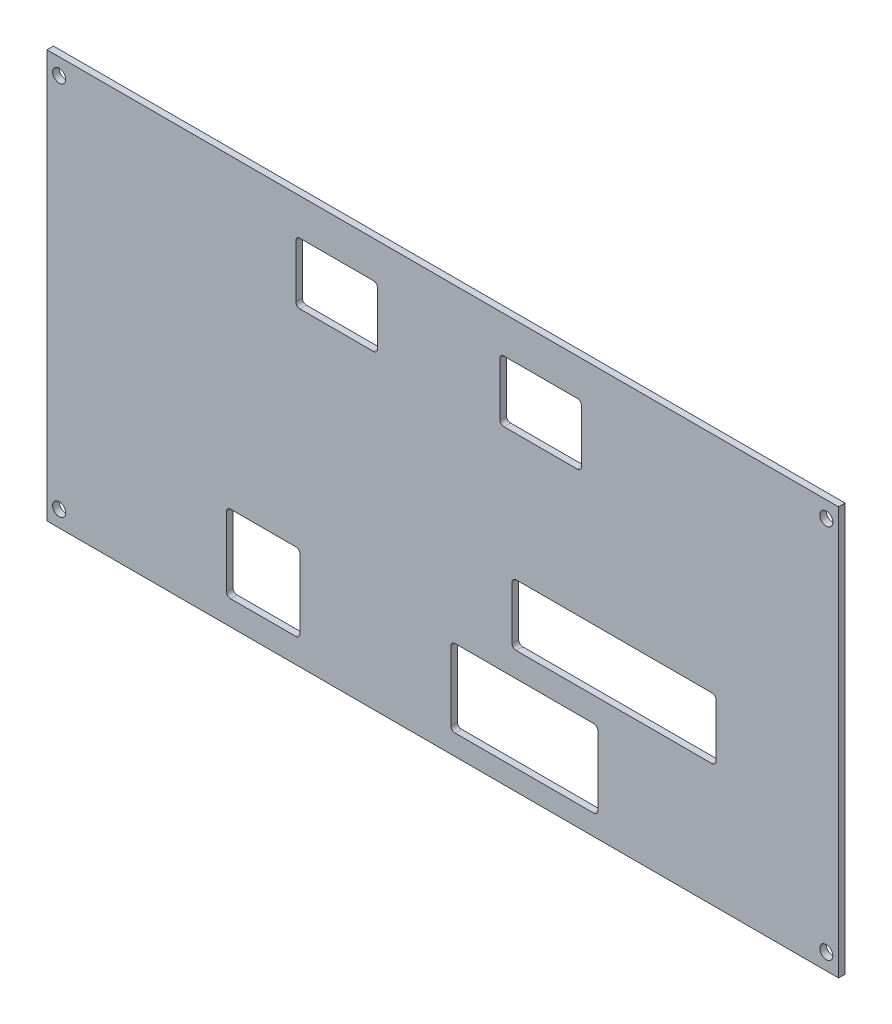
SolidWorks part; units mm, degrees
ref_plane "Plan de face" through (0, 0, 0) normal (0, 0, 1) x (1, 0, 0)
ref_plane "Plan de dessus" through (0, 0, 0) normal (0, 1, 0) x (1, 0, 0)
ref_plane "Plan de droite" through (0, 0, 0) normal (1, 0, 0) x (0, 0, -1)
sketch "Esquisse1" plane through (0, 0, 0) normal (0, 0, 1) x (1, 0, 0)
  line L1 (0, 0) -> (194, 0)
  line L2 (0, 0) -> (0, 100)
  line L3 (0, 100) -> (194, 100)
  line L4 (194, 0) -> (194, 100)
extrude "Boss.-Extru.1" add sketch "Esquisse1" along normal blind 1.6
sketch "Esquisse2" plane through (0, 0, 1.6) normal (0, 0, 1) x (1, 0, 0)
  line L0 (0, 100) -> (0, 0) construction
  line L1 (194, 0) -> (194, 100) construction
  line L2 (194, 100) -> (0, 100) construction
  line L3 (0, 0) -> (194, 0) construction
  line L5 (45, 25) -> (61, 25)
  line L6 (44, 24) -> (44, 7)
  line L7 (45, 6) -> (61, 6)
  line L8 (62, 24) -> (62, 7)
  line L9 (62, 91) -> (80, 91)
  line L10 (61, 90) -> (61, 77)
  line L11 (62, 76) -> (80, 76)
  line L12 (81, 90) -> (81, 77)
  line L13 (112, 91) -> (130, 91)
  line L14 (111, 90) -> (111, 77)
  line L15 (112, 76) -> (130, 76)
  line L16 (131, 90) -> (131, 77)
  line L17 (115, 45) -> (163, 45)
  line L18 (114, 44) -> (114, 31)
  line L19 (115, 30) -> (163, 30)
  line L20 (164, 44) -> (164, 31)
  line L21 (100, 24) -> (134, 24)
  line L22 (99, 23) -> (99, 6)
  line L23 (100, 5) -> (134, 5)
  line L24 (135, 23) -> (135, 6)
  circle A0 centre (3, 96) radius 1.6
  circle A1 centre (191, 96) radius 1.6
  circle A2 centre (191, 4) radius 1.6
  circle A3 centre (3, 4) radius 1.6
  arc A4 (44, 7) -> (45, 6) centre (45, 7) ccw
  arc A5 (61, 6) -> (62, 7) centre (61, 7) ccw
  arc A6 (61, 25) -> (62, 24) centre (61, 24) cw
  arc A7 (45, 25) -> (44, 24) centre (45, 24) ccw
  arc A8 (100, 24) -> (99, 23) centre (100, 23) ccw
  arc A9 (99, 6) -> (100, 5) centre (100, 6) ccw
  arc A10 (134, 5) -> (135, 6) centre (134, 6) ccw
  arc A11 (163, 45) -> (164, 44) centre (163, 44) cw
  arc A12 (163, 30) -> (164, 31) centre (163, 31) ccw
  arc A13 (134, 24) -> (135, 23) centre (134, 23) cw
  arc A14 (114, 31) -> (115, 30) centre (115, 31) ccw
  arc A15 (115, 45) -> (114, 44) centre (115, 44) ccw
  arc A16 (111, 77) -> (112, 76) centre (112, 77) ccw
  arc A17 (130, 76) -> (131, 77) centre (130, 77) ccw
  arc A18 (130, 91) -> (131, 90) centre (130, 90) cw
  arc A19 (112, 91) -> (111, 90) centre (112, 90) ccw
  arc A20 (61, 77) -> (62, 76) centre (62, 77) ccw
  arc A21 (80, 76) -> (81, 77) centre (80, 77) ccw
  arc A22 (80, 91) -> (81, 90) centre (80, 90) cw
  arc A23 (62, 91) -> (61, 90) centre (62, 90) ccw
  point P38 (44, 6)
  point P43 (62, 25)
  point P46 (44, 25)
  point P49 (99, 24)
  point P52 (99, 5)
  point P55 (135, 5)
  point P58 (164, 45)
  point P65 (114, 30)
  point P68 (114, 45)
  point P71 (111, 76)
  point P74 (131, 76)
  point P79 (111, 91)
  point P82 (61, 76)
  point P85 (81, 76)
  point P90 (61, 91)
  dimension "D1" = 3
  dimension "D27" = 1
  dimension "D2" = 3
  dimension "D3" = 3
  dimension "D4" = 3
  dimension "D5" = 4
  dimension "D6" = 4
  dimension "D7" = 4
  dimension "D8" = 4
  dimension "D9" = 19
  dimension "D10" = 18
  dimension "D11" = 20
  dimension "D12" = 15
  dimension "D13" = 15
  dimension "D14" = 20
  dimension "D15" = 50
  dimension "D16" = 9
  dimension "D17" = 9
  dimension "D18" = 61
  dimension "D19" = 50
  dimension "D20" = 15
  dimension "D21" = 30
  dimension "D22" = 30
  dimension "D23" = 36
  dimension "D24" = 19
  dimension "D25" = 44
  dimension "55" = 59
  dimension "D26" = 5
  dimension "D28" = 6
extrude "Enlèv. mat.-Extru.1" cut sketch "Esquisse2" against normal blind 1.6
